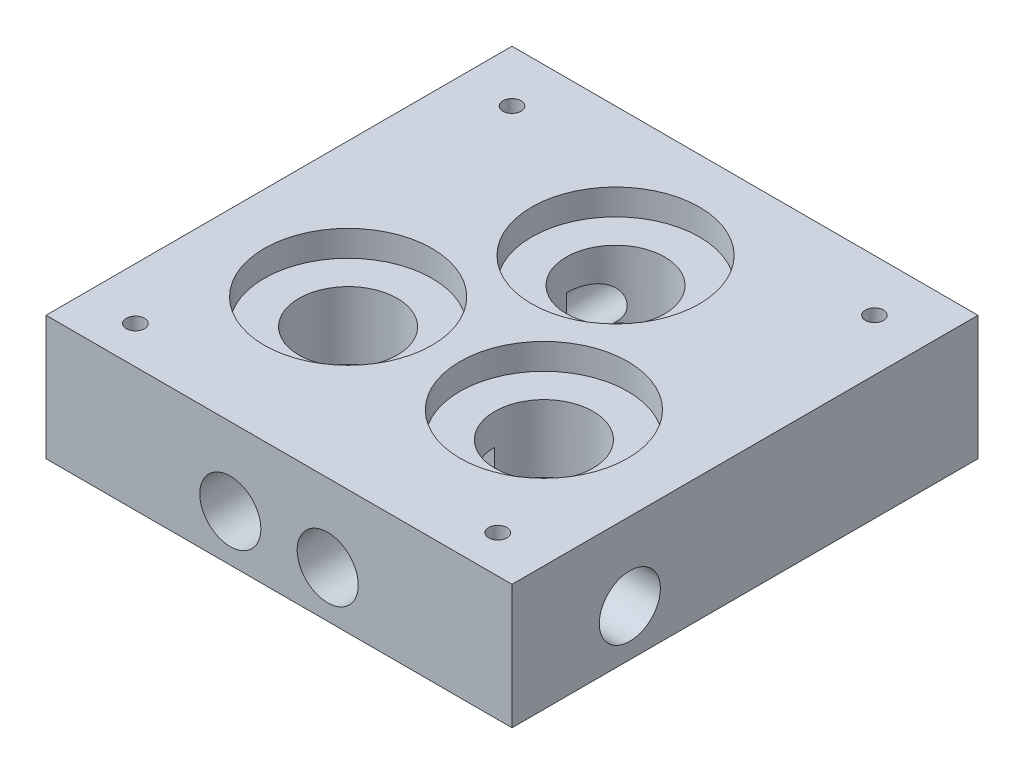
SolidWorks part; units mm, degrees
ref_plane "Front" through (0, 0, 0) normal (0, 0, 1) x (1, 0, 0)
ref_plane "Top" through (0, 0, 0) normal (0, 1, 0) x (1, 0, 0)
ref_plane "Right" through (0, 0, 0) normal (1, 0, 0) x (0, 0, -1)
sketch "Sketch1" plane through (0, 0, 0) normal (0, 1, 0) x (1, 0, 0)
  line L0 (0, 0) -> (0, 55.5185) construction
  line L1 (0, 21.8296) -> (-18.905, -10.9148) construction
  line L2 (-18.905, -10.9148) -> (18.905, -10.9148) construction
  line L3 (18.905, -10.9148) -> (0, 21.8296) construction
  line L4 (-45.003, 46.8296) -> (45.003, 46.8296)
  line L5 (-45.003, 46.8296) -> (-45.003, -43.1704)
  line L6 (-45.003, -43.1704) -> (45.003, -43.1704)
  line L7 (45.003, 46.8296) -> (45.003, -43.1704)
  line L8 (0, 0) -> (64.8649, 0) construction
  circle A0 centre (0, 0) radius 10.9148 construction
  circle A1 centre (0, 21.8296) radius 16.2
  circle A2 centre (-18.905, -10.9148) radius 16.2
  circle A3 centre (18.905, -10.9148) radius 16.2
  dimension "D2" = 32.4
  dimension "D3" = 32.4
  dimension "D4" = 32.4
  dimension "D1" = 37.81
  dimension "D5" = 26.098
  dimension "D6" = 25
  dimension "D7" = 90.006
  dimension "D8" = 90
extrude "Alphasense_housing" add sketch "Sketch1" along normal blind 5
sketch "Sketch2" plane through (0, 0, 0) normal (0, -1, 0) x (1, 0, 0)
  line L0 (0, -12.3296) -> (-45.003, -12.3296) construction
  line L1 (-45.003, 43.1704) -> (45.003, 43.1704)
  line L2 (-45.003, 43.1704) -> (-45.003, -46.8296)
  line L3 (-45.003, -46.8296) -> (45.003, -46.8296)
  line L4 (45.003, 43.1704) -> (45.003, -46.8296)
  line L5 (9.405, 10.9148) -> (9.405, 43.1704) construction
  line L6 (-9.405, 10.9148) -> (-9.405, 43.1704) construction
  line L7 (-18.905, 20.4148) -> (-45.003, 20.4148) construction
  line L8 (18.905, 20.4148) -> (45.003, 20.4148) construction
  line L9 (-9.5, -21.8296) -> (-9.5, -46.8296) construction
  circle A0 centre (-18.905, 10.9148) radius 9.5
  circle A1 centre (18.905, 10.9148) radius 9.5
  circle A2 centre (0, -21.8296) radius 9.5
  dimension "D1" = 19
extrude "Chamber_housing" add sketch "Sketch2" along normal blind 13
sketch "Sketch3" plane through (0, -13, 0) normal (0, -1, 0) x (1, 0, 0)
  line L1 (-45.003, 43.1704) -> (45.003, 43.1704)
  line L2 (-45.003, 43.1704) -> (-45.003, -46.8296)
  line L3 (-45.003, -46.8296) -> (45.003, -46.8296)
  line L4 (45.003, 43.1704) -> (45.003, -46.8296)
extrude "Base" add sketch "Sketch3" along normal blind 6
ref_plane "Drills_plane" through (0, -10, 0) normal (0, 1, 0) x (1, 0, 0)
sketch "Drills_sketch" plane through (0, -10, 0) normal (0, 1, 0) x (1, 0, 0)
  line L0 (-45.003, -20.4148) -> (-18.905, -20.4148) construction
  line L1 (-9.405, -43.1704) -> (-9.405, -10.9148) construction
  line L2 (9.405, -43.1704) -> (9.405, -10.9148) construction
  line L3 (18.905, -20.4148) -> (45.003, -20.4148) construction
  line L4 (0, 12.3296) -> (-45.003, 12.3296) construction
  line L5 (-9.5, 46.8296) -> (-9.5, 21.8296) construction
  point P24 (0, 0)
  point P25 (0, 0)
  point P26 (0, 0)
  point P27 (0, 0)
  point P28 (0, 0)
  point P29 (0, 0)
  point P30 (0, 0)
sketch "Sketch5" plane through (-45.003, 0, 0) normal (-1, 0, 0) x (0, 0, 1)
  circle A0 centre (20.4148, -10) radius 5.9
  dimension "D1" = 11.8
extrude "Drill" cut sketch "Sketch5" against normal blind 10 contours A0
sketch "Sketch6" plane through (0, 0, 43.1704) normal (0, 0, 1) x (1, 0, 0)
  circle A0 centre (-9.405, -10) radius 5.9
  dimension "D1" = 11.8
extrude "Drill2" cut sketch "Sketch6" against normal blind 10
sketch "Sketch7" plane through (0, 0, 43.1704) normal (0, 0, 1) x (1, 0, 0)
  circle A0 centre (9.405, -10) radius 5.9
  dimension "D1" = 11.8
extrude "Drill3" cut sketch "Sketch7" against normal blind 10
sketch "Sketch8" plane through (45.003, 0, 0) normal (1, 0, 0) x (0, 0, -1)
  circle A0 centre (-20.4148, -10) radius 5.9
  dimension "D1" = 11.8
extrude "InletDrill" cut sketch "Sketch8" against normal blind 10
sketch "Sketch10" plane through (-45.003, 0, 0) normal (-1, 0, 0) x (0, 0, 1)
  circle A0 centre (-12.3296, -10) radius 5.9
  dimension "D1" = 11.8
extrude "Drill5" cut sketch "Sketch10" against normal blind 10
sketch "Sketch11" plane through (0, 0, -46.8296) normal (0, 0, -1) x (-1, 0, 0)
  circle A0 centre (9.5, -10) radius 5.9
  dimension "D1" = 11.8
extrude "OutleDrill" cut sketch "Sketch11" against normal blind 10
sketch "Sketch12" plane through (0, 5, 0) normal (0, 1, 0) x (1, 0, 0)
  line L0 (0, 0) -> (0, -22.3558) construction
  line L1 (0, 0) -> (19.6803, 11.3624) construction
  line L2 (0, 0) -> (-21.2385, 10.3587) construction
  line L3 (-35, 36.8296) -> (-35, -35.9148) construction
  line L4 (-35, -35.9148) -> (35, -35.9148) construction
  line L5 (35, -35.9148) -> (35, 36.8296) construction
  line L6 (35, 36.8296) -> (-35, 36.8296) construction
  line L7 (0, 46.8296) -> (0, -43.1704) construction
  line L8 (-45.003, 46.8296) -> (45.003, 46.8296) construction
  line L9 (-45.003, -43.1704) -> (45.003, -43.1704) construction
  line L10 (-45.003, 1.8296) -> (45.003, 1.8296) construction
  line L11 (-45.003, 46.8296) -> (-45.003, -43.1704) construction
  line L12 (45.003, 46.8296) -> (45.003, -43.1704) construction
  circle A0 centre (0, -22.3558) radius 1.25 construction
  circle A1 centre (19.6803, 11.3624) radius 1.25 construction
  circle A2 centre (-21.2385, 10.3587) radius 1.25 construction
  circle A3 centre (-35, 36.8296) radius 1.75
  circle A4 centre (35, 36.8296) radius 1.75
  circle A5 centre (-35, -35.9148) radius 1.75
  circle A6 centre (35, -35.9148) radius 1.75
  dimension "D1" = 2.5
  dimension "D4" = 3.5
  dimension "D2" = 22.3558
  dimension "D3" = 22.7248
  dimension "D5" = 120
  dimension "D6" = 23.63
  dimension "D7" = 116
  dimension "D8" = 35
  dimension "D9" = 35
  dimension "D10" = 15
  dimension "D11" = 25
  dimension "D12" = 10
  dimension "D13" = 7.2556
  dimension "D14" = 72.7444
extrude "ClippingThreads" cut sketch "Sketch12" against normal blind 10
sketch "Sketch13" plane through (-35.003, 0, 0) normal (-1, 0, 0) x (0, 0, 1)
  circle A0 centre (-12.3296, -10) radius 4
  dimension "D1" = 8
extrude "Cut-Extrude1" cut sketch "Sketch13" against normal up to vertex (35.003 mm away) up to point (0, -10, -12.3296)
sketch "Sketch14" plane through (-35.003, 0, 0) normal (-1, 0, 0) x (0, 0, 1)
  circle A0 centre (20.4148, -10) radius 4
  dimension "D1" = 8
extrude "Cut-Extrude2" cut sketch "Sketch14" against normal up to vertex (16.098 mm away) up to point (-18.905, -10, 20.4148)
sketch "Sketch15" plane through (0, 0, 33.1704) normal (0, 0, 1) x (1, 0, 0)
  circle A0 centre (-9.405, -10) radius 4
  dimension "D1" = 8
extrude "Cut-Extrude3" cut sketch "Sketch15" against normal up to vertex (22.2556 mm away) up to point (-9.405, -10, 10.9148)
sketch "Sketch16" plane through (0, 0, 33.1704) normal (0, 0, 1) x (1, 0, 0)
  circle A0 centre (9.405, -10) radius 4
  dimension "D1" = 8
extrude "Cut-Extrude4" cut sketch "Sketch16" against normal up to vertex (22.2556 mm away) up to point (9.405, -10, 10.9148)
sketch "Sketch17" plane through (35.003, 0, 0) normal (1, 0, 0) x (0, 0, -1)
  circle A0 centre (-20.4148, -10) radius 4
  dimension "D1" = 8
extrude "Cut-Extrude5" cut sketch "Sketch17" against normal up to vertex (16.098 mm away) up to point (18.905, -10, 20.4148)
sketch "Sketch18" plane through (0, 0, -36.8296) normal (0, 0, -1) x (-1, 0, 0)
  circle A0 centre (9.5, -10) radius 4
  dimension "D1" = 8
extrude "Cut-Extrude6" cut sketch "Sketch18" against normal up to vertex (15 mm away) up to point (-9.5, -10, -21.8296)
equation "\"d_racor\"= 11.8"
equation "\"D1@Sketch5\"=\"d_racor\""
equation "\"h_alphasense\"= 5"
equation "\"D1@Sketch6\"=\"d_racor\""
equation "\"D1@Alphasense_housing\" = \"h_alphasense\""
equation "\"h_chamber\"= 13"
equation "\"D1@Chamber_housing\" = \"h_chamber\""
equation "\"d_alphasense\" = 32.4mm"
equation "\"d_chamber\"= 19"
equation "\"h_base\"= 25 - \"h_chamber\" - \"h_alphasense\"-1"
equation "\"d_thread\"= 2.5"
equation "\"D1@Sketch12\"=\"d_thread\""
equation "\"length_thread\"=10"
equation "\"D1@ClippingThreads\" = \"length_thread\""
equation "\"D2@Sketch1\"=\"d_alphasense\""
equation "\"D3@Sketch1\"=\"d_alphasense\""
equation "\"D4@Sketch1\"=\"d_alphasense\""
equation "\"D1@Sketch2\"=\"d_chamber\""
equation "\"D1@Sketch8\"=\"d_racor\""
equation "\"D1@Sketch11\"=\"d_racor\""
equation "\"D1@Sketch10\"=\"d_racor\""
equation "\"D1@Sketch7\"=\"d_racor\""
equation "\"D1@Base\"=\"h_base\""
equation "\"D4@Sketch12\"=\"clip_thread_tap_drill\""
equation "\"length_racor\"= 10"
equation "\"D1@OutleDrill\"=\"length_racor\""
equation "\"D1@InletDrill\"=\"length_racor\""
equation "\"D1@Drill3\"=\"length_racor\""
equation "\"D1@Drill2\"=\"length_racor\""
equation "\"D1@Drill5\"=\"length_racor\""
equation "\"D1@Drill\"=\"length_racor\""
equation "\"d_pipe\"=8"
equation "\"D1@Sketch13\"=\"d_pipe\""
equation "\"D1@Sketch14\"=\"d_pipe\""
equation "\"D1@Sketch15\"=\"d_pipe\""
equation "\"D1@Sketch16\"=\"d_pipe\""
equation "\"D1@Sketch17\"=\"d_pipe\""
equation "\"clip_thread_hole\" = 4"
equation "\"clip_thread_tap_drill\" = 3.5"
